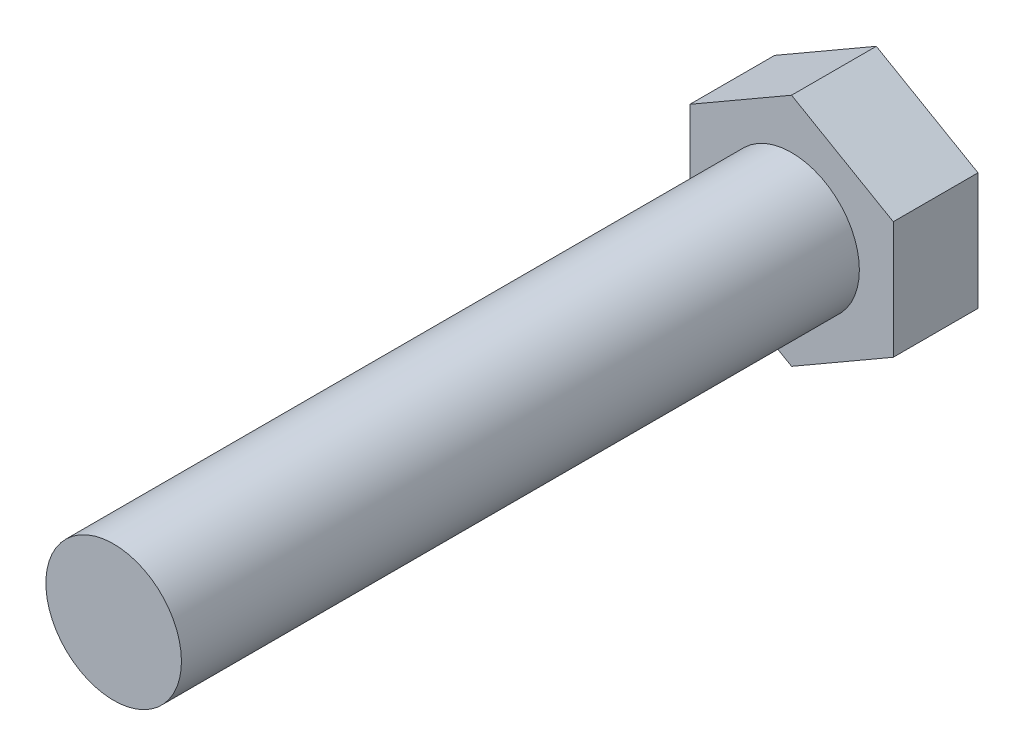
SolidWorks part; units mm, degrees
ref_plane "Přední rovina" through (0, 0, 0) normal (0, 0, 1) x (1, 0, 0)
ref_plane "Vrchní rovina" through (0, 0, 0) normal (0, 1, 0) x (1, 0, 0)
ref_plane "Pravá rovina" through (0, 0, 0) normal (1, 0, 0) x (0, 0, -1)
sketch "Skica1" plane through (0, 0, 0) normal (0, 0, 1) x (1, 0, 0)
  line L1 (15, 8.6603) -> (0, 17.3205)
  line L2 (0, 17.3205) -> (-15, 8.6603)
  line L3 (-15, 8.6603) -> (-15, -8.6603)
  line L4 (-15, -8.6603) -> (0, -17.3205)
  line L5 (0, -17.3205) -> (15, -8.6603)
  line L6 (15, -8.6603) -> (15, 8.6603)
  circle A0 centre (0, 0) radius 15 construction
  point P1 (0, 0)
  dimension "D1" = 30
extrude "Přidat vysunutím1" add sketch "Skica1" along normal blind 12.5
sketch "Skica2" plane through (0, 0, 12.5) normal (0, 0, 1) x (1, 0, 0)
  circle A0 centre (0, 0) radius 10
  dimension "D1" = 20
extrude "Přidat vysunutím2" add sketch "Skica2" along normal blind 100
sketch "Skica3" plane through (0, 0, 0) normal (0, 0, -1) x (-1, 0, 0)
  line L0 (-15, -8.6603) -> (-15, 8.6603) construction
  circle A0 centre (0, 0) radius 15
